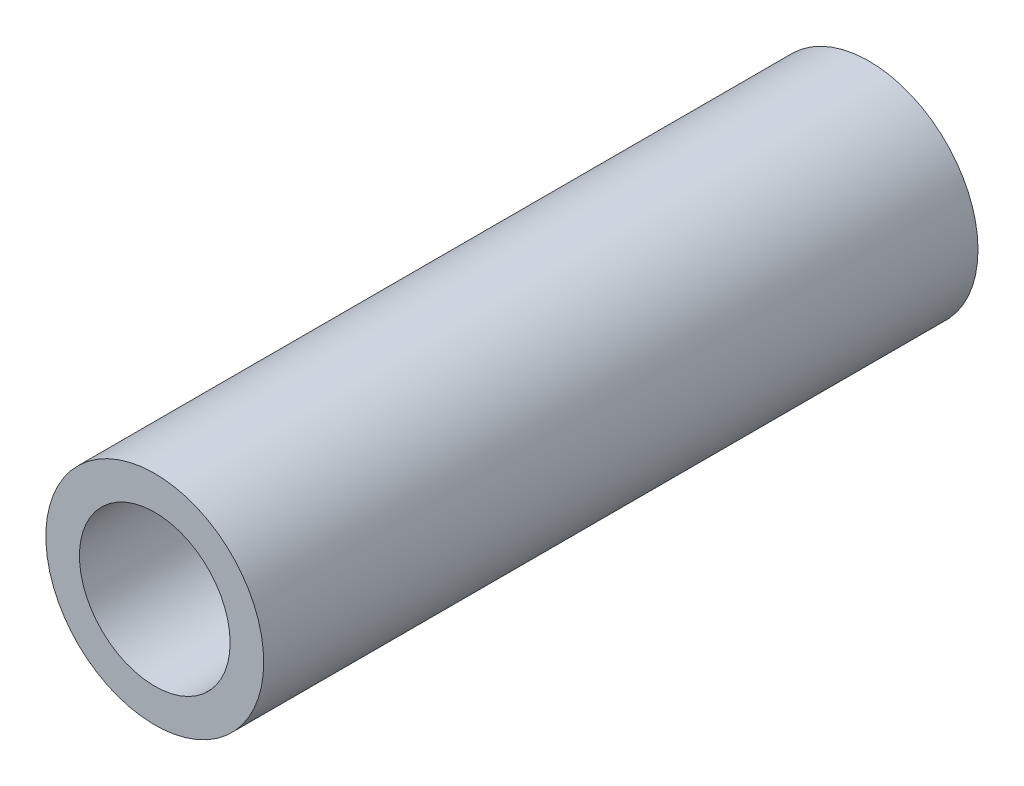
SolidWorks part; units mm, degrees
material "PVC Rigid"
ref_plane "Front Plane" through (0, 0, 0) normal (0, 0, 1) x (1, 0, 0)
ref_plane "Top Plane" through (0, 0, 0) normal (0, 1, 0) x (1, 0, 0)
ref_plane "Right Plane" through (0, 0, 0) normal (1, 0, 0) x (0, 0, -1)
sketch "Sketch1" plane through (0, 0, 0) normal (0, 0, 1) x (1, 0, 0)
  circle A0 centre (0, 0) radius 7.747
  circle A1 centre (0, 0) radius 5.3594
  dimension "D1" = 15.494
  dimension "D2" = 10.7188
extrude "Boss-Extrude1" add sketch "Sketch1" along normal blind 50.8
